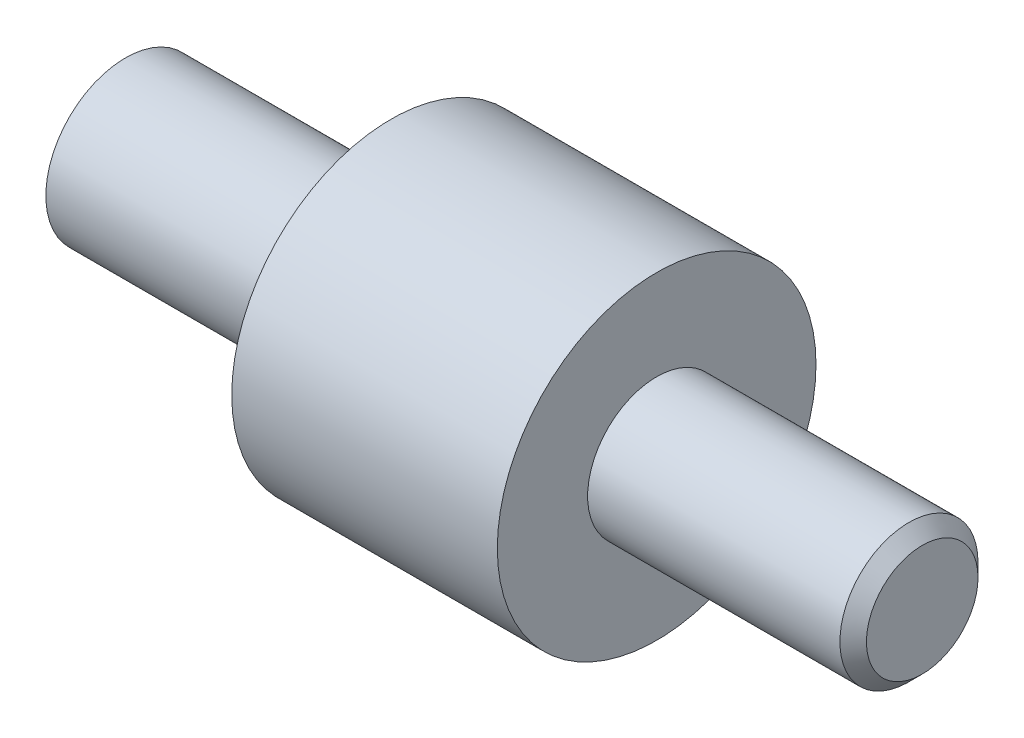
SolidWorks part; units mm, degrees
ref_plane "Plan de face" through (0, 0, 0) normal (0, 0, 1) x (1, 0, 0)
ref_plane "Plan de dessus" through (0, 0, 0) normal (0, 1, 0) x (1, 0, 0)
ref_plane "Plan de droite" through (0, 0, 0) normal (1, 0, 0) x (0, 0, -1)
sketch "Esquisse1" plane through (0, 0, 0) normal (0, 0, 1) x (1, 0, 0)
  line L0 (0, 0) -> (0, 1.5)
  line L1 (0, 1.5) -> (5, 1.5)
  line L2 (5, 1.5) -> (5, 3)
  line L3 (5, 3) -> (10, 3)
  line L4 (10, 3) -> (10, 1.3)
  line L5 (10, 1.3) -> (15, 1.3)
  line L6 (15, 1.3) -> (15, 0)
  line L7 (15, 0) -> (0, 0)
  dimension "D1" = 1.5
  dimension "D2" = 1.3
  dimension "D3" = 3
  dimension "D4" = 5
  dimension "D5" = 5
  dimension "D6" = 5
revolve "Révolution1" add sketch "Esquisse1" angle 360 about L7
chamfer "Chanfrein1" distance 0.25 angle 45 1 edges at (15, 0, -1.3)
